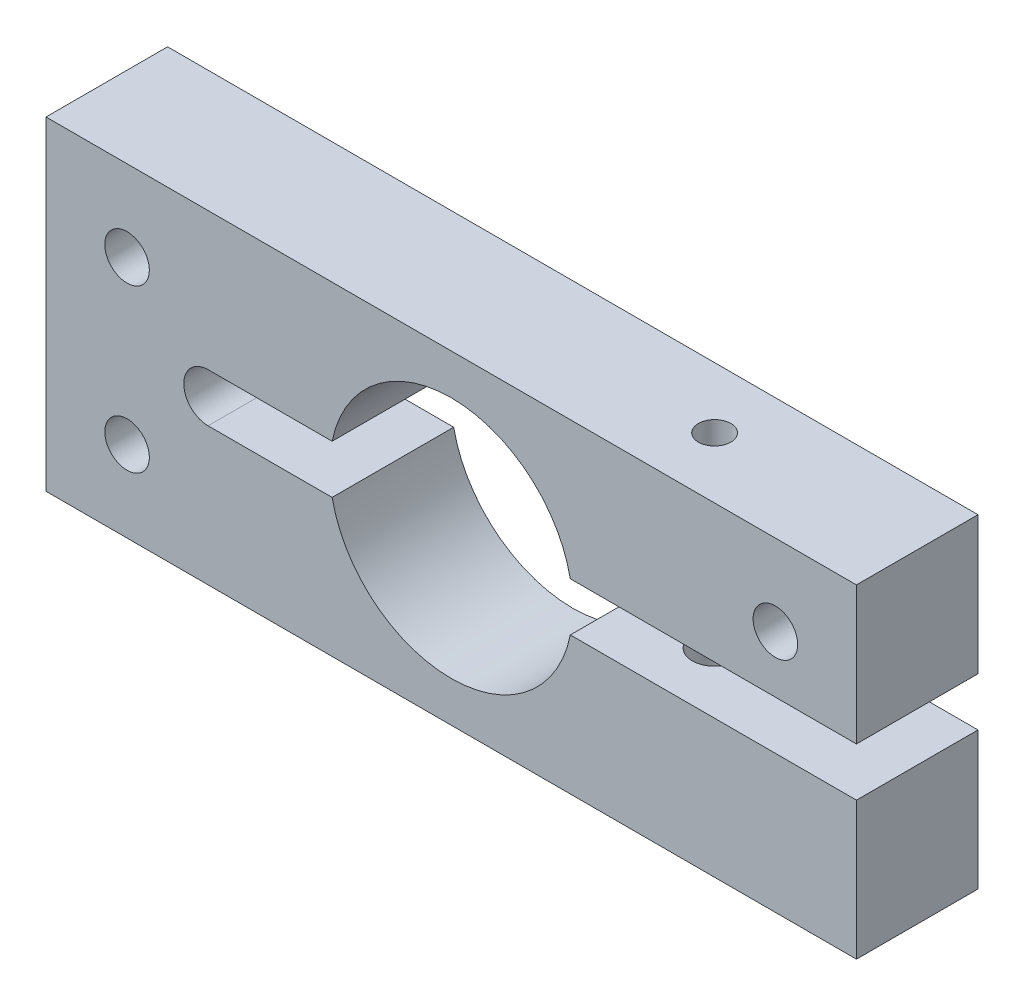
SolidWorks part; units mm, degrees
material "1060 Alloy"
ref_plane "Front Plane" through (0, 0, 0) normal (0, 0, 1) x (1, 0, 0)
ref_plane "Top Plane" through (0, 0, 0) normal (0, 1, 0) x (1, 0, 0)
ref_plane "Right Plane" through (0, 0, 0) normal (1, 0, 0) x (0, 0, -1)
sketch "Sketch1" plane through (0, 0, 0) normal (0, 0, 1) x (1, 0, 0)
  line L0 (0, 20) -> (100, 20) construction
  line L1 (0, 0) -> (100, 0)
  line L2 (0, 0) -> (0, 40)
  line L3 (0, 40) -> (100, 40)
  line L4 (100, 0) -> (100, 17)
  line L5 (20, 20) -> (100, 20) construction
  line L6 (20, 23) -> (35.3031, 23)
  line L7 (20, 17) -> (35.3031, 17)
  line L8 (64.6969, 23) -> (100, 23)
  line L9 (64.6969, 17) -> (100, 17)
  line L10 (100, 23) -> (100, 40)
  line L11 (50, 20) -> (50, 40) construction
  line L12 (10, 30) -> (10, 20) construction
  line L13 (90, 30) -> (90, 0) construction
  line L17 (10, 10) -> (90, 10) construction
  arc A0 (64.6969, 23) -> (35.3031, 23) centre (50, 20) ccw
  arc A1 (20, 23) -> (20, 17) centre (20, 20) ccw
  circle A2 centre (10, 30) radius 2.75
  arc A3 (35.3031, 17) -> (64.6969, 17) centre (50, 20) ccw
  circle A4 centre (10, 10) radius 2.75
  circle A5 centre (90, 30) radius 2.75
  dimension "D3" = 30
  dimension "D4" = 3
  dimension "D9" = 5.5
  dimension "D1" = 100
  dimension "D2" = 40
  dimension "D5" = 80
  dimension "D6" = 50
  dimension "D7" = 10
  dimension "D8" = 10
extrude "Boss-Extrude1" add sketch "Sketch1" along normal blind 15
sketch "Sketch2" plane through (0, 0, 0) normal (0, -1, 0) x (1, 0, 0)
  line L0 (0, 7.5) -> (100, 7.5) construction
  line L1 (0, 15) -> (0, 0) construction
  line L2 (100, 15) -> (100, 0) construction
  circle A0 centre (75, 7.5) radius 2
  dimension "D2" = 4
  dimension "D1" = 25
extrude "Cut-Extrude1" cut sketch "Sketch2" against normal through all
sketch "Sketch3" plane through (0, 0, 0) normal (0, -1, 0) x (1, 0, 0)
  circle A0 centre (75, 7.5) radius 4.5
  dimension "D1" = 9
extrude "Cut-Extrude2" cut sketch "Sketch3" against normal blind 5
sketch "Sketch4" plane through (0, 0, 0) normal (0, 0, 1) x (1, 0, 0)
  line L0 (0, 20) -> (17, 20) construction
  line L1 (0, 40) -> (0, 0) construction
  line L2 (50, 40) -> (50, 0) construction
  line L3 (100, 40) -> (0, 40) construction
  line L4 (0, 0) -> (100, 0) construction
  circle A0 centre (10, 10) radius 4.5
  arc A1 (20, 23) -> (20, 17) centre (20, 20) ccw construction
  circle A2 centre (10, 30) radius 4.5
  circle A3 centre (90, 30) radius 4.5
  dimension "D1" = 9
extrude "Cut-Extrude3" cut sketch "Sketch4" along normal blind 5
sketch "Sketch5" plane through (0, 5, 0) normal (0, -1, 0) x (1, 0, 0)
  circle A0 centre (75, 7.5) radius 2.75
  dimension "D1" = 5.5
extrude "Cut-Extrude4" cut sketch "Sketch5" against normal up to next
